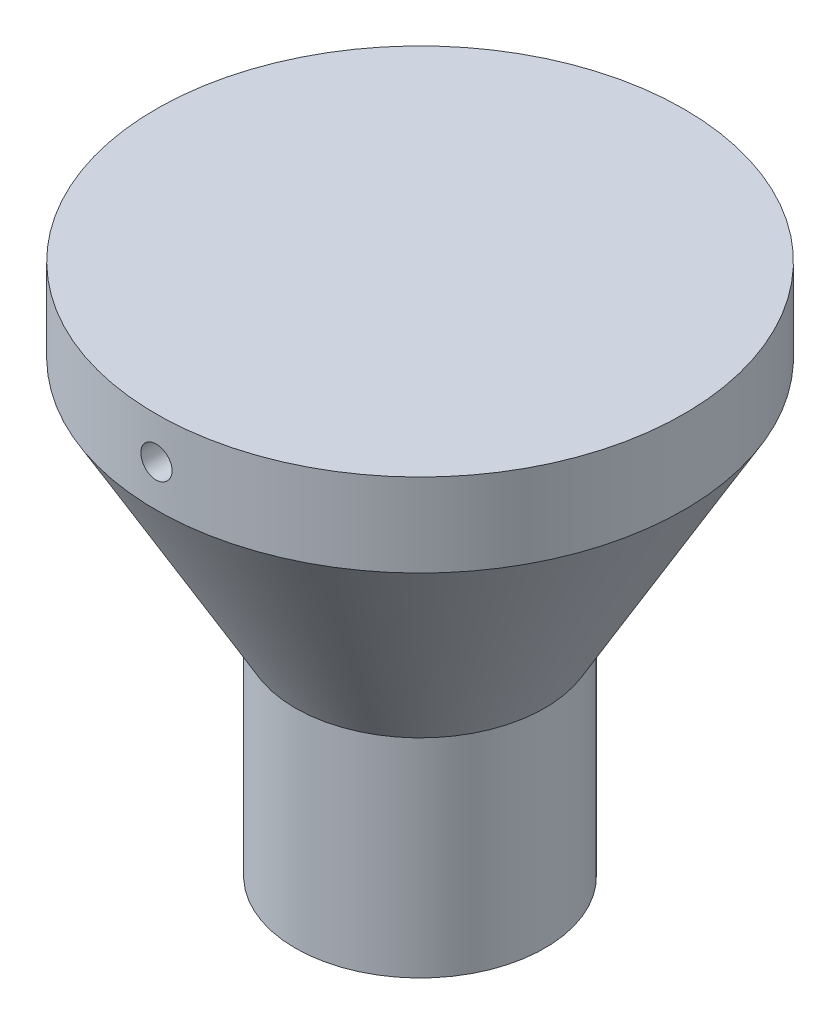
SolidWorks part; units mm, degrees
ref_plane "Front Plane" through (0, 0, 0) normal (0, 0, 1) x (1, 0, 0)
ref_plane "Top Plane" through (0, 0, 0) normal (0, 1, 0) x (1, 0, 0)
ref_plane "Right Plane" through (0, 0, 0) normal (1, 0, 0) x (0, 0, -1)
sketch "Sketch1" plane through (0, 0, 0) normal (0, 0, 1) x (1, 0, 0)
  line L0 (0, 0) -> (0, 88)
  line L1 (0, 0) -> (-30, 0)
  line L2 (-30, 0) -> (-30, 50)
  line L3 (-30, 50) -> (-63.4863, 108)
  line L5 (-63.4863, 108) -> (-63.4863, 128)
  line L6 (-63.4863, 128) -> (0, 128)
  line L7 (0, 128) -> (0, 88)
  dimension "D1" = 88
  dimension "D2" = 30
  dimension "D3" = 50
  dimension "D4" = 150
  dimension "D5" = 20
  dimension "D6" = 63.4863
revolve "Revolve1" add sketch "Sketch1" angle 360 about L0
shell "Shell1" thickness 7.5
sketch "Sketch2" plane through (0, 0, 0) normal (0, -1, 0) x (1, 0, 0)
  circle A1 centre (0, 0) radius 28.25
  circle A2 centre (0, 0) radius 24
  dimension "D1" = 56.5
  dimension "D2" = 48
extrude "Cut-Extrude1" cut sketch "Sketch2" against normal blind 2
sketch "Sketch4" plane through (0, 0, 0) normal (0, 0, 1) x (1, 0, 0)
  line L0 (0, 128) -> (0, 108) construction
  line L1 (63.4863, 128) -> (-63.4863, 128) construction
  line L2 (63.4863, 108) -> (-63.4863, 108) construction
  circle A0 centre (0, 118) radius 3.75
  dimension "D1" = 7.5
extrude "Cut-Extrude2" cut sketch "Sketch4" against normal mid plane 150
